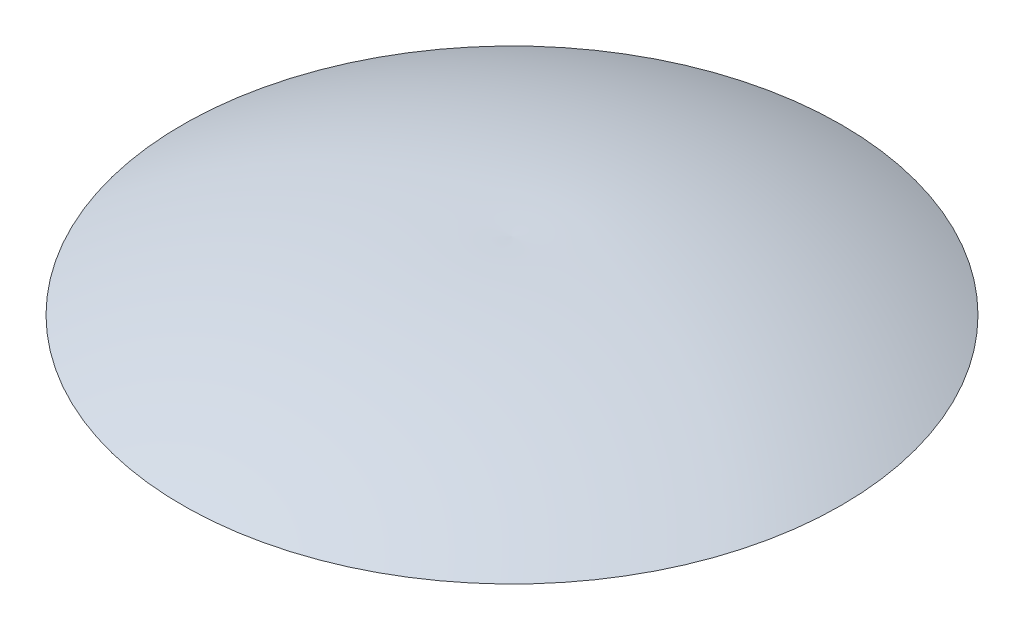
SolidWorks part; units mm, degrees
ref_plane "Front Plane" through (0, 0, 0) normal (0, 0, 1) x (1, 0, 0)
ref_plane "Top Plane" through (0, 0, 0) normal (0, 1, 0) x (1, 0, 0)
ref_plane "Right Plane" through (0, 0, 0) normal (1, 0, 0) x (0, 0, -1)
sketch "Sketch1" plane through (0, 0, 0) normal (0, 0, 1) x (1, 0, 0)
  line L0 (0, 0) -> (34.925, 0)
  line L1 (0, 0) -> (0, 12.7)
  line L3 (34.925, 0) -> (44.45, 12.7)
  line L4 (0, 12.7) -> (0, 31.75)
  line L6 (0, 31.75) -> (0, 50.8)
  spline S0 degree 2 poles (44.45, 12.7) (69.7506, 18.1599) (92.075, 31.75) knots 0 0 0 1 1 1
  spline S1 degree 2 poles (92.075, 31.75) (49.2369, 53.1166) (0, 50.8) knots 0 0 0 1 1 1
revolve "Revolve1" add sketch "Sketch1" angle 360 about L6
hole_wizard "5/8-11 Tapped Hole1" positions "Sketch3" profile "Sketch2" tap size "5/8-11" standard "ANSI Inch"
sketch "Sketch3" plane through (0, 0, 0) normal (0, -1, 0) x (-1, 0, 0)
  point P0 (0, 0)
sketch "Sketch2" plane through (0, 0, 0) normal (1, 0, 0) x (0, 0, -1)
  line L0 (0, 0) -> (0, 23.1035)
  line L1 (0, 23.1035) -> (6.7462, 19.05)
  line L2 (6.7462, 19.05) -> (6.7462, 0)
  line L5 (6.7462, 0) -> (0, 0)
  line L10 (0, 23.1035) -> (-6.7462, 19.05) construction
  line L11 (0, -6.35) -> (0, 107.95) construction
  dimension "Tap Drill Dia." = 13.4925
  dimension "Tap Drill Depth" = 19.05
  dimension "Drill Angle" = 118
cosmetic thread "Hole Thread1" parameters "D1"=19.05, "D2"=15.875
hole_wizard "3/16 (0.1875) Diameter Hole1" positions "3DSketch2" profile "Sketch5" hole size "3/16" standard "ANSI Inch"
sketch3d "3DSketch2"
  point P0 (-39.2467, 5.8384, 2.1169)
sketch "Sketch5" plane through (-39.2467, 5.8384, 2.1169) normal (-0.4422, 0.6342, 0.6342) x (0.4079, -0.4876, 0.7719)
  line L0 (0, 0) -> (0, 14.1308)
  line L1 (0, 14.1308) -> (2.3812, 12.7)
  line L2 (2.3812, 12.7) -> (2.3812, 0)
  line L5 (2.3812, 0) -> (0, 0)
  line L10 (0, 14.1308) -> (-2.3813, 12.7) construction
  line L11 (0, -6.35) -> (0, 107.95) construction
  dimension "Hole Dia." = 4.7625
  dimension "Hole Depth" = 12.7
  dimension "Drill Angle" = 118
